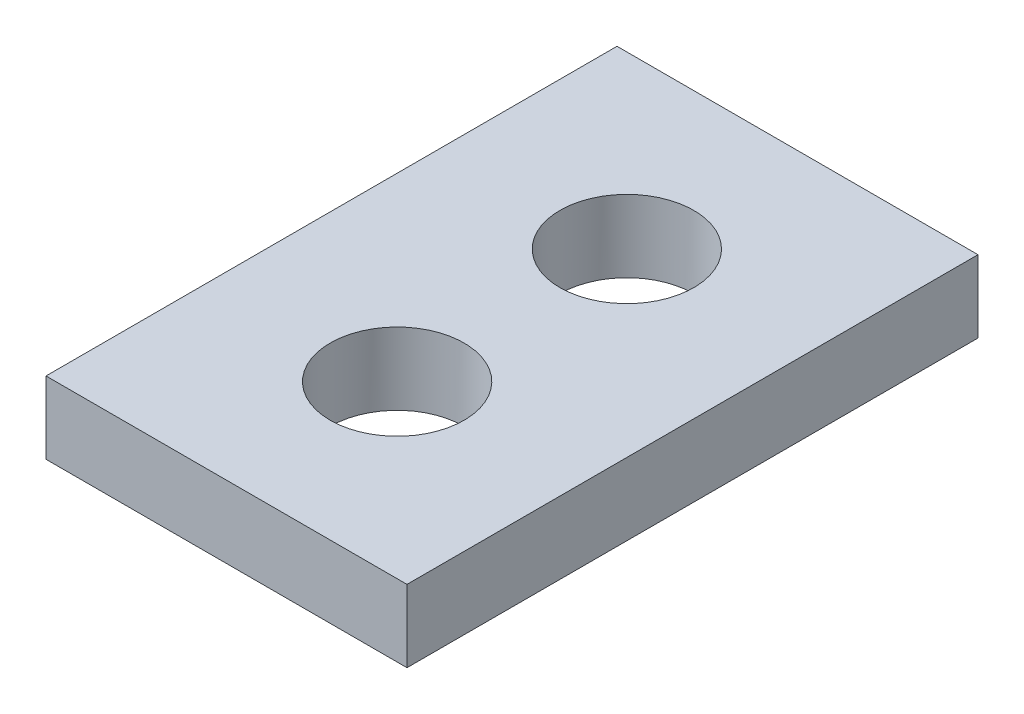
SolidWorks part; units mm, degrees
ref_plane "Front Plane" through (0, 0, 0) normal (0, 0, 1) x (1, 0, 0)
ref_plane "Top Plane" through (0, 0, 0) normal (0, 1, 0) x (1, 0, 0)
ref_plane "Right Plane" through (0, 0, 0) normal (1, 0, 0) x (0, 0, -1)
sketch "Sketch1" plane through (0, 0, 0) normal (0, 1, 0) x (1, 0, 0)
  line L1 (-6.875, -10.875) -> (6.875, -10.875)
  line L2 (-6.875, -10.875) -> (-6.875, 10.875)
  line L3 (-6.875, 10.875) -> (6.875, 10.875)
  line L4 (6.875, -10.875) -> (6.875, 10.875)
  line L5 (-6.875, -10.875) -> (6.875, 10.875) construction
  line L6 (-6.875, 10.875) -> (6.875, -10.875) construction
  point P0 (0, 0)
  dimension "D1" = 13.75
  dimension "D2" = 21.75
extrude "Boss-Extrude1" add sketch "Sketch1" along normal blind 2.75
sketch "Sketch2" plane through (0, 2.75, 0) normal (0, 1, 0) x (1, 0, 0)
  line L0 (0, -4.375) -> (0, 4.375) construction
  circle A0 centre (0, 4.375) radius 2.55
  circle A1 centre (0, -4.375) radius 2.55
  point P4 (0, 0)
  dimension "D1" = 5.1
  dimension "D2" = 8.75
extrude "Cut-Extrude1" cut sketch "Sketch2" against normal blind 10
sketch "Sketch4" plane through (0, 0, 0) normal (0, -1, 0) x (1, 0, 0)
  line L0 (6.875, 10.875) -> (6.875, -10.875) construction
  line L1 (5.975, -8.5) -> (6.875, -8.5)
  line L2 (5.975, -8.5) -> (5.975, 8.5)
  line L3 (5.975, 8.5) -> (6.875, 8.5)
  line L4 (6.875, -8.5) -> (6.875, 8.5)
  line L5 (5.975, -8.5) -> (6.875, 8.5) construction
  line L6 (5.975, 8.5) -> (6.875, -8.5) construction
  point P0 (6.425, 0)
  dimension "D1" = 0.9
  dimension "D2" = 17
extrude "Boss-Extrude3" [suppressed] add sketch "Sketch4" along normal blind 2
